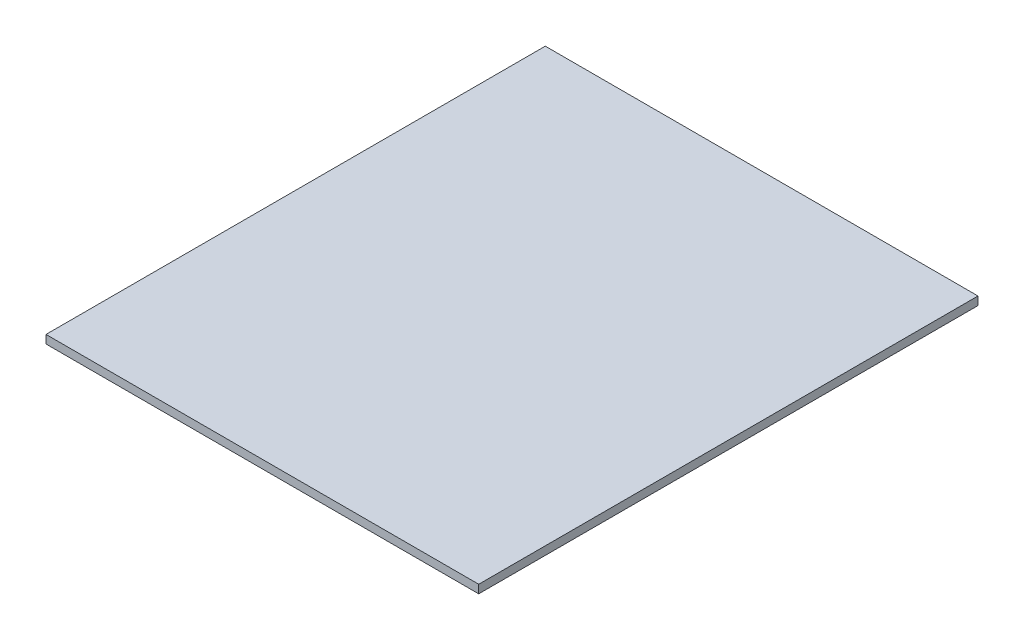
SolidWorks part; units mm, degrees
ref_plane "Front Plane" through (0, 0, 0) normal (0, 0, 1) x (1, 0, 0)
ref_plane "Top Plane" through (0, 0, 0) normal (0, 1, 0) x (1, 0, 0)
ref_plane "Right Plane" through (0, 0, 0) normal (1, 0, 0) x (0, 0, -1)
sketch "Sketch1" plane through (0, 0, 0) normal (0, 1, 0) x (1, 0, 0)
  line L1 (-65, -75) -> (65, -75)
  line L2 (-65, -75) -> (-65, 75)
  line L3 (-65, 75) -> (65, 75)
  line L4 (65, -75) -> (65, 75)
  line L5 (-65, -75) -> (65, 75) construction
  line L6 (-65, 75) -> (65, -75) construction
  point P0 (0, 0)
  dimension "D1" = 130
  dimension "D2" = 150
extrude "Boss-Extrude1" add sketch "Sketch1" along normal blind 2.5
